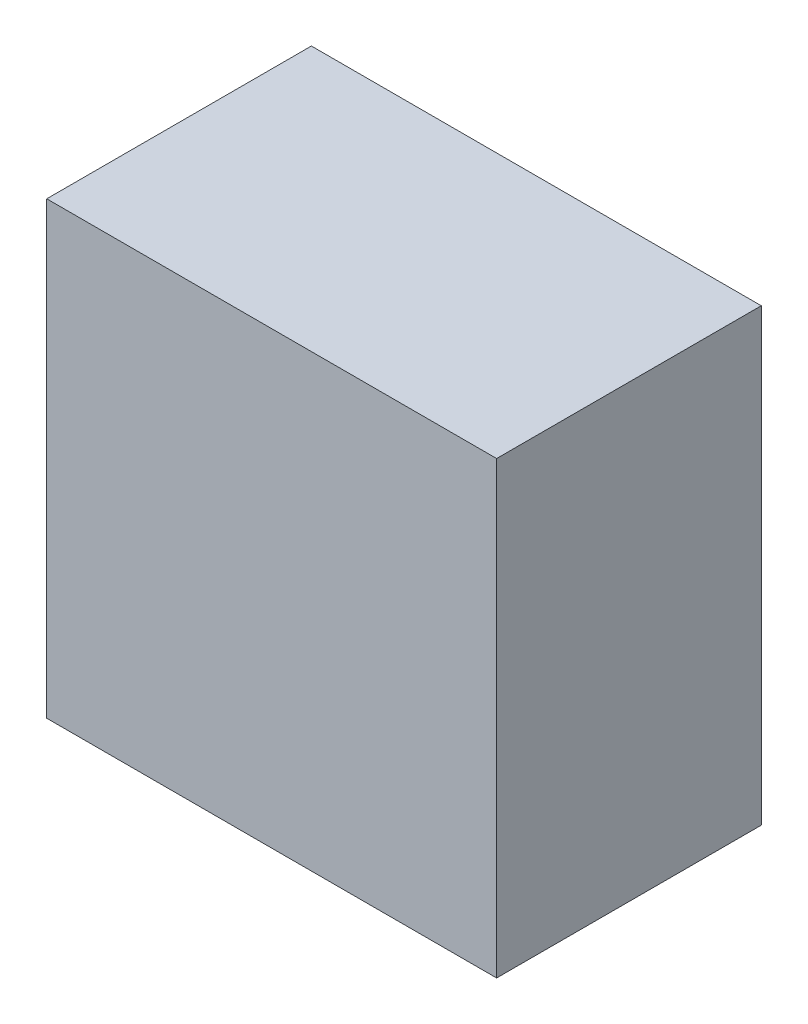
SolidWorks part; units mm, degrees
ref_plane "Front Plane" through (0, 0, 0) normal (0, 0, 1) x (1, 0, 0)
ref_plane "Top Plane" through (0, 0, 0) normal (0, 1, 0) x (1, 0, 0)
ref_plane "Right Plane" through (0, 0, 0) normal (1, 0, 0) x (0, 0, -1)
sketch "Sketch1" plane through (0, 0, 0) normal (0, 0, 1) x (1, 0, 0)
  line L1 (-9.8276, 14.931) -> (7.1724, 14.931)
  line L2 (-9.8276, 14.931) -> (-9.8276, -2.069)
  line L3 (-9.8276, -2.069) -> (7.1724, -2.069)
  line L4 (7.1724, 14.931) -> (7.1724, -2.069)
  dimension "D1" = 17
  dimension "D2" = 17
extrude "Boss-Extrude1" add sketch "Sketch1" along normal blind 10
